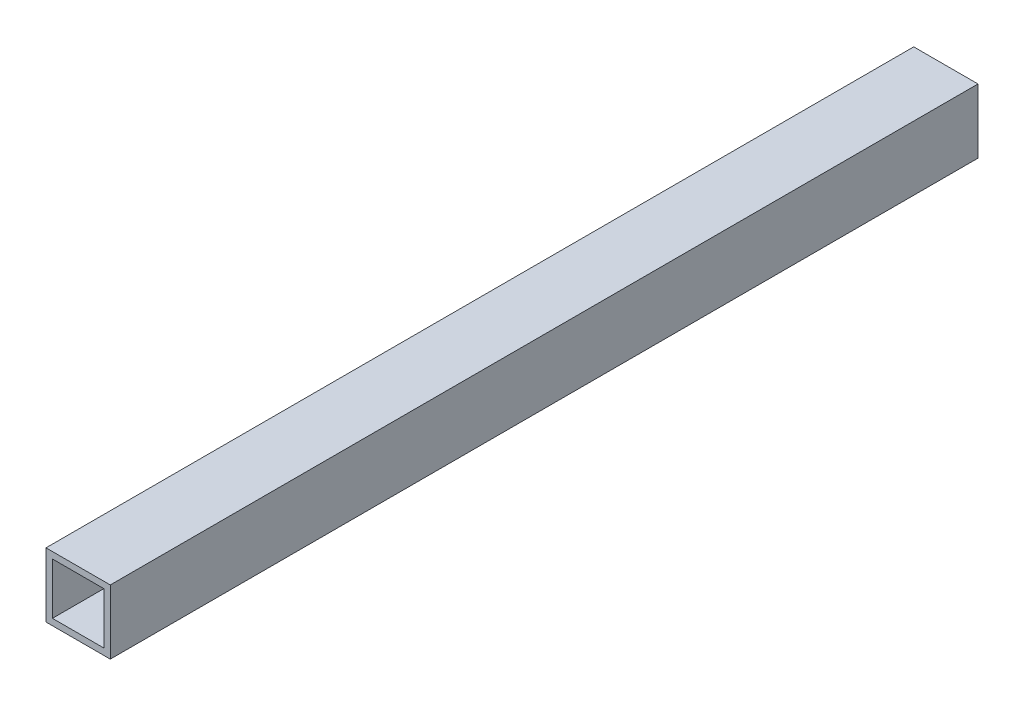
SolidWorks part; units mm, degrees
ref_plane "Front Plane" through (0, 0, 0) normal (0, 0, 1) x (1, 0, 0)
ref_plane "Top Plane" through (0, 0, 0) normal (0, 1, 0) x (1, 0, 0)
ref_plane "Right Plane" through (0, 0, 0) normal (1, 0, 0) x (0, 0, -1)
sketch "Sketch1" plane through (0, 0, 0) normal (0, 0, 1) x (1, 0, 0)
  line L0 (-12.7, 12.7) -> (12.7, 12.7)
  line L1 (-15.875, 15.875) -> (15.875, 15.875)
  line L2 (-15.875, 15.875) -> (-15.875, -15.875)
  line L3 (-15.875, -15.875) -> (15.875, -15.875)
  line L4 (15.875, 15.875) -> (15.875, -15.875)
  line L5 (12.7, 12.7) -> (12.7, -12.7)
  line L6 (-12.7, -12.7) -> (12.7, -12.7)
  line L7 (-12.7, 12.7) -> (-12.7, -12.7)
  dimension "D1" = 31.75
  dimension "D2" = 31.75
  dimension "D3" = 15.875
  dimension "D4" = 15.875
  dimension "D5" = 3.175
extrude "Extrude1" add sketch "Sketch1" along normal blind 428.625
